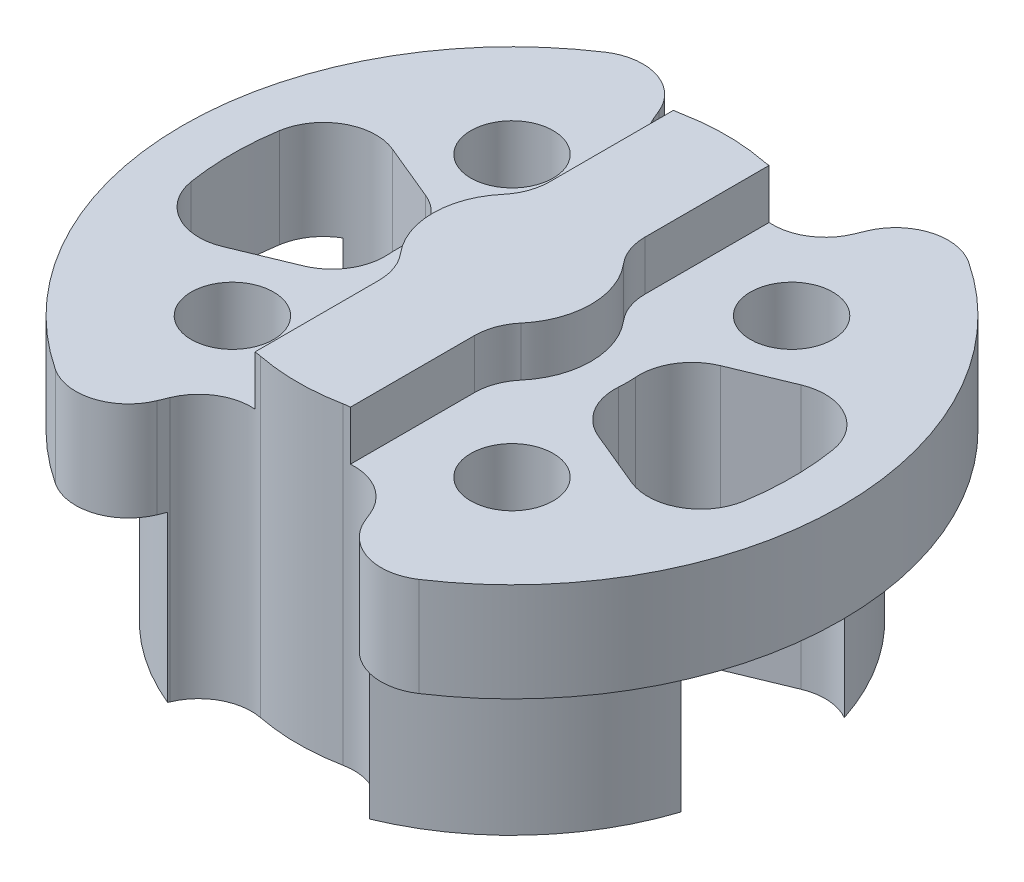
SolidWorks part; units mm, degrees
ref_plane "Front Plane" through (0, 0, 0) normal (0, 0, 1) x (1, 0, 0)
ref_plane "Top Plane" through (0, 0, 0) normal (0, 1, 0) x (1, 0, 0)
ref_plane "Right Plane" through (0, 0, 0) normal (1, 0, 0) x (0, 0, -1)
sketch "Sketch1" plane through (0, 0, 0) normal (0, 1, 0) x (1, 0, 0)
  circle A0 centre (0, 0) radius 10
  dimension "D1" = 20
extrude "Boss-Extrude1" add sketch "Sketch1" along normal blind 8
sketch "Sketch4" plane through (0, 8, 0) normal (0, 1, 0) x (1, 0, 0)
  line L0 (-1.45, 6.3362) -> (-1.45, 1.9125)
  line L2 (1.45, 1.9125) -> (1.45, 6.3362)
  line L3 (-1.45, -1.9125) -> (-1.45, -6.3362)
  line L5 (1.45, -1.9125) -> (1.45, -6.3362)
  arc A0 (-1.45, 6.3362) -> (1.45, 6.3362) centre (0, 0) cw
  circle A1 centre (0, 0) radius 3 construction
  arc A2 (1.45, -1.9125) -> (1.45, 1.9125) centre (0, 0) ccw
  arc A8 (-1.45, -6.3362) -> (1.45, -6.3362) centre (0, 0) ccw
  arc A9 (-1.45, 1.9125) -> (-1.45, -1.9125) centre (0, 0) ccw
  circle A10 centre (0, 0) radius 6.5 construction
  dimension "D1" = 2.9
  dimension "D3" = 13
  dimension "D2" = 2.4
  dimension "D4" = 6
extrude "Boss-Extrude2" add sketch "Sketch4" along normal blind 1.5
fillet "Fillet1" radius 1.6 4 edges at (-1.45, 8.75, 1.9125) (1.45, 8.75, 1.9125) (1.45, 8.75, -1.9125) (-1.45, 8.75, -1.9125)
sketch "Sketch5" plane through (0, 0, 0) normal (0, 1, 0) x (1, 0, 0)
  circle A0 centre (0, 0) radius 8
  circle A1 centre (0, 0) radius 10
  circle A2 centre (0, 0) radius 10 construction
  dimension "D1" = 16
extrude "Cut-Extrude1" cut sketch "Sketch5" along normal offset from surface (5 mm away) 3 up to face at (0, 8, 0)
sketch "Sketch6" plane through (0, 0, 0) normal (0, -1, 0) x (1, 0, 0)
  line L0 (0, 0) -> (4.2426, 4.2426) construction
  line L1 (-1000, 0) -> (49000, 0) construction
  circle A0 centre (0, 0) radius 6 construction
  circle A1 centre (4.2426, 4.2426) radius 1.25
  dimension "D1" = 12
  dimension "D2" = 45
  dimension "D3" = 2.5
extrude "Cut-Extrude2" cut sketch "Sketch6" against normal up to next
pattern_circular "CirPattern1" count 4 over 360 about axis through (0, 0, 0) along (0, 1, 0) of "Cut-Extrude2"
sketch "Sketch7" plane through (0, 8, 0) normal (0, 1, 0) x (1, 0, 0)
  line L0 (-7.853, -3.2528) -> (0, 0) construction
  line L1 (0, 0) -> (-7.853, 3.2528) construction
  line L2 (0, 0) -> (-3.8268, 9.2388) construction
  line L3 (0, 0) -> (3.8268, 9.2388) construction
  line L4 (-3.2336, -1.3394) -> (-7.853, -3.2528)
  line L5 (-3.2336, 1.3394) -> (-7.853, 3.2528)
  line L6 (-2.4874, 6.0052) -> (-3.8268, 9.2388)
  line L7 (2.4874, 6.0052) -> (3.8268, 9.2388)
  arc A0 (-7.853, -3.2528) -> (-7.853, 3.2528) centre (0, 0) cw
  arc A1 (-3.8268, 9.2388) -> (3.8268, 9.2388) centre (0, 0) cw
  arc A2 (-3.2336, -1.3394) -> (-3.2336, 1.3394) centre (0, 0) cw
  arc A3 (-2.4874, 6.0052) -> (2.4874, 6.0052) centre (0, 0) cw
  circle A4 centre (0, 0) radius 10 construction
  arc A5 (1.45, 6.3362) -> (-1.45, 6.3362) centre (0, 0) ccw construction
  dimension "D1" = 1.5
  dimension "D2" = 5
  dimension "D5" = 45
  dimension "D4" = 45
extrude "Cut-Extrude3" cut sketch "Sketch7" against normal through all
fillet "Fillet2" radius 1.6 8 edges at (-7.853, 6.5, 3.2528) (-7.853, 6.5, -3.2528) (-3.2336, 4, 1.3394) (-3.2336, 4, -1.3394) (2.4874, 4, -6.0052) (-2.4874, 4, -6.0052) (3.8268, 6.5, -9.2388) (-3.8268, 6.5, -9.2388)
pattern_circular "CirPattern2" count 2 over 360 about axis through (0, 0, 0) along (0, 1, 0) of "Cut-Extrude3", "Fillet2"
